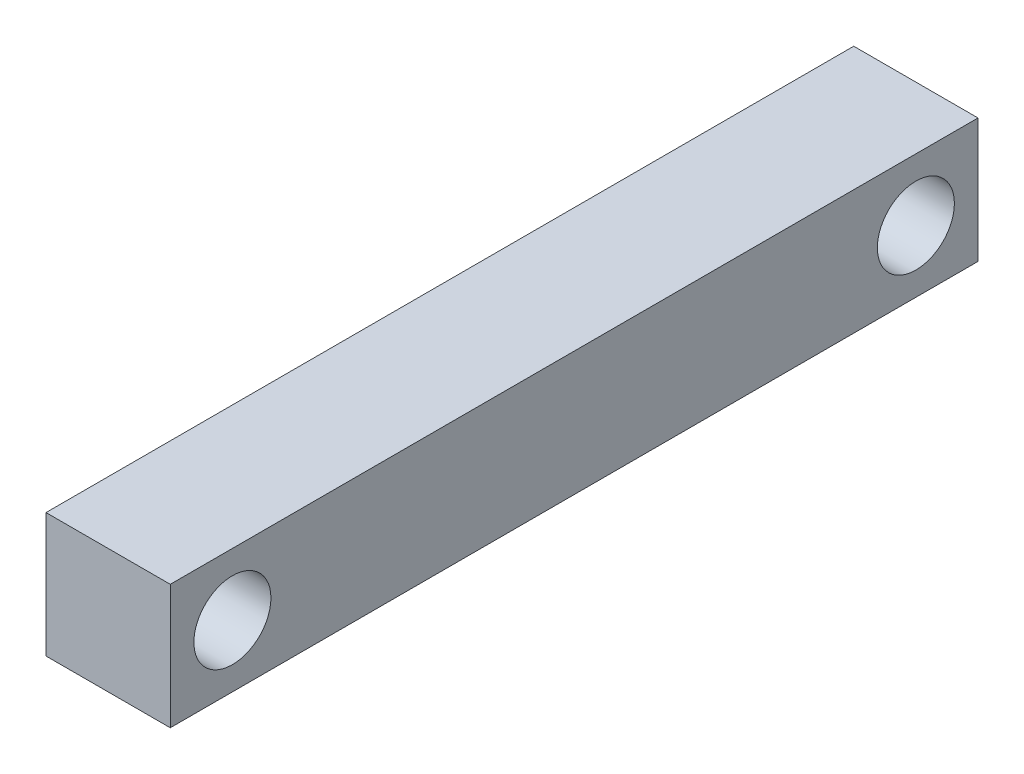
SolidWorks part; units mm, degrees
material "7075-T6 (SN)"
ref_plane "Front" through (0, 0, 0) normal (0, 0, 1) x (1, 0, 0)
ref_plane "Top" through (0, 0, 0) normal (0, 1, 0) x (1, 0, 0)
ref_plane "Right" through (0, 0, 0) normal (1, 0, 0) x (0, 0, -1)
sketch "Sketch1" plane through (0, 0, 0) normal (1, 0, 0) x (0, 0, -1)
  line L0 (0, 0) -> (50000, 0) construction
  line L1 (-32.5, 5) -> (32.5, 5)
  line L2 (-32.5, 5) -> (-32.5, -5)
  line L3 (-32.5, -5) -> (32.5, -5)
  line L4 (32.5, 5) -> (32.5, -5)
  line L5 (-32.5, 5) -> (32.5, -5) construction
  line L6 (-32.5, -5) -> (32.5, 5) construction
  circle A0 centre (-27.5, 0) radius 3.1
  circle A1 centre (27.5, 0) radius 3.1
  point P0 (0, 0)
  dimension "D3" = 6.2
  dimension "D4" = 6.2
  dimension "D1" = 10
  dimension "D2" = 65
  dimension "D5" = 5
  dimension "D6" = 5
extrude "Boss-Extrude1" add sketch "Sketch1" along normal blind 10
